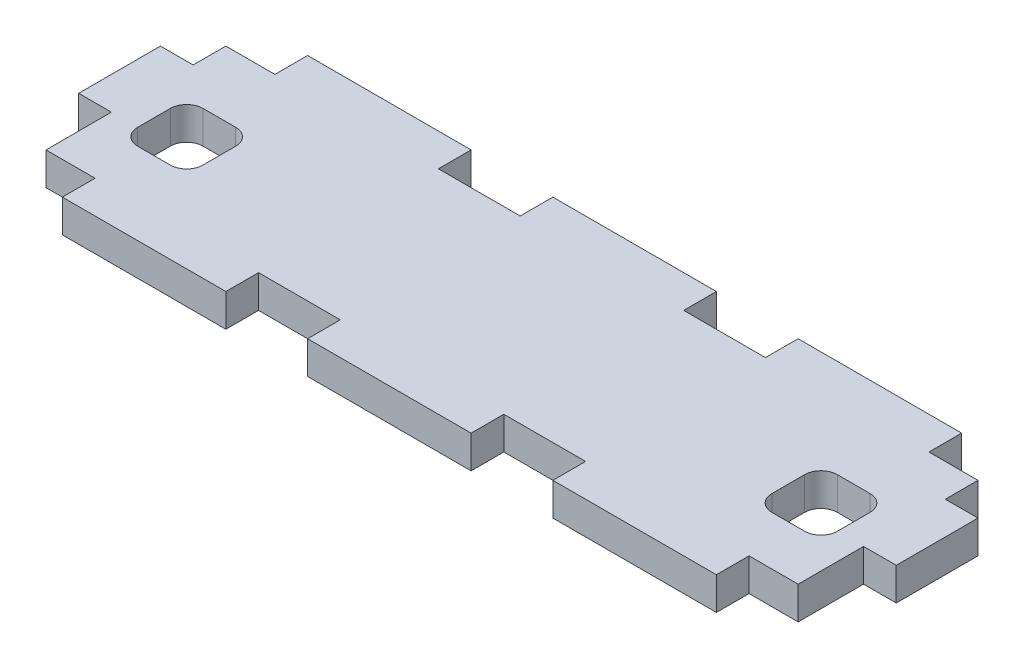
SolidWorks part; units mm, degrees
ref_plane "Front Plane" through (0, 0, 0) normal (0, 0, 1) x (1, 0, 0)
ref_plane "Top Plane" through (0, 0, 0) normal (0, 1, 0) x (1, 0, 0)
ref_plane "Right Plane" through (0, 0, 0) normal (1, 0, 0) x (0, 0, -1)
sketch "Sketch1" plane through (0, 0, 0) normal (0, 1, 0) x (1, 0, 0)
  line L1 (63.5, -19.05) -> (-63.5, -19.05)
  line L2 (63.5, -19.05) -> (63.5, 19.05)
  line L3 (63.5, 19.05) -> (-63.5, 19.05)
  line L4 (-63.5, -19.05) -> (-63.5, 19.05)
  line L5 (63.5, -19.05) -> (-63.5, 19.05) construction
  line L6 (63.5, 19.05) -> (-63.5, -19.05) construction
  point P0 (0, 0)
  dimension "D1" = 127
  dimension "D2" = 38.1
extrude "Boss-Extrude1" add sketch "Sketch1" along normal mid plane 5.08
sketch "Sketch2" plane through (0, 2.54, 0) normal (0, 1, 0) x (1, 0, 0)
  line L0 (63.5, 19.05) -> (-63.5, 19.05) construction
  line L1 (-63.5, 19.05) -> (-58.42, 19.05)
  line L2 (-63.5, 19.05) -> (-63.5, 8.89)
  line L3 (-63.5, 8.89) -> (-58.42, 8.89)
  line L4 (-58.42, 19.05) -> (-58.42, 8.89)
  line L5 (-63.5, 19.05) -> (-58.42, 8.89) construction
  line L6 (-63.5, 8.89) -> (-58.42, 19.05) construction
  line L7 (-63.5, 19.05) -> (-63.5, -19.05) construction
  line L8 (-63.5, -19.05) -> (63.5, -19.05) construction
  line L9 (-63.5, -3.81) -> (-58.42, -3.81)
  line L10 (-63.5, -3.81) -> (-63.5, -19.05)
  line L11 (-63.5, -19.05) -> (-58.42, -19.05)
  line L12 (-58.42, -3.81) -> (-58.42, -19.05)
  line L13 (-63.5, -3.81) -> (-58.42, -19.05) construction
  line L14 (-63.5, -19.05) -> (-58.42, -3.81) construction
  point P0 (-60.96, 13.97)
  point P9 (-60.96, -11.43)
  dimension "D1" = 5.08
  dimension "D2" = 10.16
  dimension "D3" = 12.7
  dimension "D4" = 5.08
extrude "Cut-Extrude1" cut sketch "Sketch2" against normal blind 5.08
mirror "Mirror1" about plane through (0, 0, 0) normal (1, 0, 0) of "Cut-Extrude1"
sketch "Sketch3" plane through (0, 2.54, 0) normal (0, 1, 0) x (1, 0, 0)
  line L0 (-58.42, -19.05) -> (58.42, -19.05) construction
  line L1 (-63.5, -13.97) -> (-50.8, -13.97)
  line L2 (-63.5, -13.97) -> (-63.5, -19.05)
  line L3 (-63.5, -19.05) -> (-50.8, -19.05)
  line L4 (-50.8, -13.97) -> (-50.8, -19.05)
  line L5 (-63.5, -13.97) -> (-50.8, -19.05) construction
  line L6 (-63.5, -19.05) -> (-50.8, -13.97) construction
  line L7 (-63.5, 8.89) -> (-63.5, -3.81) construction
  point P0 (-57.15, -16.51)
  dimension "D1" = 5.08
  dimension "D2" = 0
  dimension "D3" = 12.7
extrude "Cut-Extrude2" cut sketch "Sketch3" against normal up to surface (5.08 mm away) up to face at (0, -2.54, -1.6933)
mirror "Mirror2" about plane through (0, 0, 0) normal (1, 0, 0) of "Cut-Extrude2"
sketch "Sketch4" plane through (0, 2.54, 0) normal (0, 1, 0) x (1, 0, 0)
  line L0 (-50.8, -19.05) -> (50.8, -19.05) construction
  line L1 (-25.4, -13.97) -> (-12.7, -13.97)
  line L2 (-25.4, -13.97) -> (-25.4, -19.05)
  line L3 (-25.4, -19.05) -> (-12.7, -19.05)
  line L4 (-12.7, -13.97) -> (-12.7, -19.05)
  line L5 (-25.4, -13.97) -> (-12.7, -19.05) construction
  line L6 (-25.4, -19.05) -> (-12.7, -13.97) construction
  line L7 (-50.8, -19.05) -> (-50.8, -13.97) construction
  point P0 (-19.05, -16.51)
  dimension "D1" = 25.4
  dimension "D2" = 12.7
  dimension "D3" = 5.08
extrude "Cut-Extrude4" cut sketch "Sketch4" against normal up to surface (5.08 mm away) up to face at (0, -2.54, 2.2225)
pattern_linear "LPattern1" count 2 spacing 38.1 along (1, 0, 0) of "Cut-Extrude4"
sketch "Sketch7" plane through (0, 2.54, 0) normal (0, 1, 0) x (1, 0, 0)
  line L0 (58.42, 19.05) -> (-58.42, 19.05) construction
  line L1 (-58.42, 19.05) -> (58.42, 19.05)
  line L2 (-58.42, 19.05) -> (-58.42, 13.97)
  line L3 (-58.42, 13.97) -> (58.42, 13.97)
  line L4 (58.42, 19.05) -> (58.42, 13.97)
  line L5 (-58.42, 8.89) -> (-58.42, 19.05) construction
  line L6 (58.42, 8.89) -> (58.42, 19.05) construction
  dimension "D1" = 5.08
extrude "Cut-Extrude7" cut sketch "Sketch7" against normal up to surface (5.08 mm away) up to face at (0, -2.54, 6.985)
sketch "Sketch8" plane through (0, 2.54, 0) normal (0, 1, 0) x (1, 0, 0)
  line L0 (-58.42, 13.97) -> (58.42, 13.97) construction
  line L1 (-50.8, 19.05) -> (-25.4, 19.05)
  line L2 (-50.8, 19.05) -> (-50.8, 13.97)
  line L3 (-50.8, 13.97) -> (-25.4, 13.97)
  line L4 (-25.4, 19.05) -> (-25.4, 13.97)
  line L6 (-50.8, -19.05) -> (-50.8, -13.97) construction
  line L8 (-25.4, -13.97) -> (-25.4, -19.05) construction
  line L9 (-12.7, -19.05) -> (-12.7, -13.97) construction
  line L10 (-12.7, 13.97) -> (12.7, 13.97)
  line L11 (-12.7, 13.97) -> (-12.7, 19.05)
  line L12 (-12.7, 19.05) -> (12.7, 19.05)
  line L13 (12.7, 13.97) -> (12.7, 19.05)
  line L14 (12.7, -13.97) -> (12.7, -19.05) construction
  line L15 (25.4, -19.05) -> (25.4, -13.97) construction
  line L16 (25.4, 13.97) -> (50.8, 13.97)
  line L17 (25.4, 13.97) -> (25.4, 19.05)
  line L18 (25.4, 19.05) -> (50.8, 19.05)
  line L19 (50.8, 13.97) -> (50.8, 19.05)
  line L20 (50.8, -19.05) -> (50.8, -13.97) construction
  dimension "D1" = 5.08
  dimension "D2" = 0
  dimension "D3" = 0
  dimension "D4" = 0
  dimension "D5" = 0
  dimension "D6" = 5.08
  dimension "D7" = 0
  dimension "D8" = 0
  dimension "D9" = 5.08
extrude "Boss-Extrude2" add sketch "Sketch8" against normal up to surface (5.08 mm away) up to face at (0, -2.54, 7.4083)
sketch "Sketch9" plane through (0, 2.54, 0) normal (0, 1, 0) x (1, 0, 0)
  line L0 (-50.8, -13.97) -> (-58.42, -13.97) construction
  line L1 (-51.8074, 3.81) -> (-46.7274, 3.81)
  line L2 (-54.3474, 1.27) -> (-54.3474, -3.81)
  line L3 (-51.8074, -6.35) -> (-46.7274, -6.35)
  line L4 (-44.1874, 1.27) -> (-44.1874, -3.81)
  line L5 (-63.5, 8.89) -> (-63.5, -3.81) construction
  arc A0 (-46.7274, -6.35) -> (-44.1874, -3.81) centre (-46.7274, -3.81) ccw
  arc A1 (-54.3474, -3.81) -> (-51.8074, -6.35) centre (-51.8074, -3.81) ccw
  arc A2 (-51.8074, 3.81) -> (-54.3474, 1.27) centre (-51.8074, 1.27) ccw
  arc A3 (-46.7274, 3.81) -> (-44.1874, 1.27) centre (-46.7274, 1.27) cw
  point P10 (-44.1874, -6.35)
  point P15 (-54.3474, 3.81)
  point P18 (-44.1874, 3.81)
  dimension "D5" = 2.54
  dimension "D1" = 10.16
  dimension "D2" = 10.16
  dimension "D3" = 7.62
  dimension "D4" = 9.1526
extrude "Cut-Extrude8" cut sketch "Sketch9" against normal up to surface (5.08 mm away)
mirror "Mirror3" about plane through (0, 0, 0) normal (1, 0, 0) of "Cut-Extrude8"
